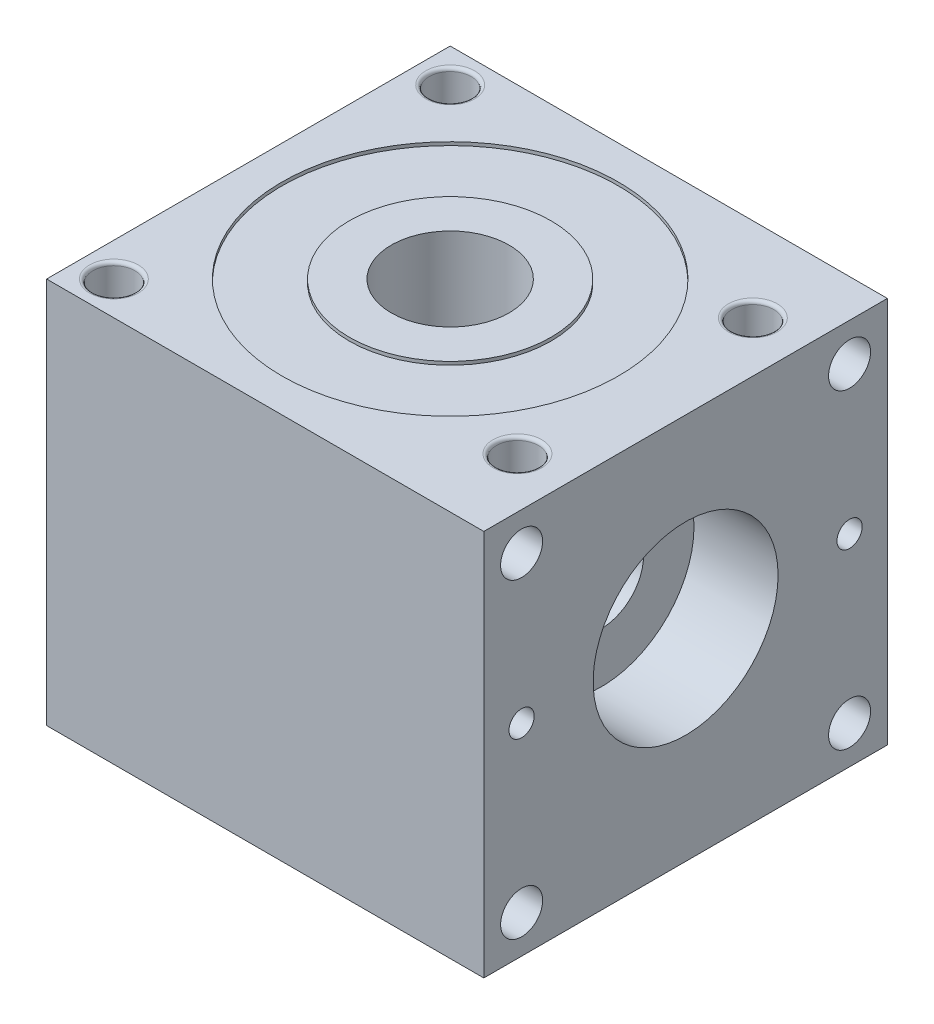
SolidWorks part; units mm, degrees
material "7079 Alloy"
ref_plane "Front Plane" through (0, 0, 0) normal (0, 0, 1) x (1, 0, 0)
ref_plane "Top Plane" through (0, 0, 0) normal (0, 1, 0) x (1, 0, 0)
ref_plane "Right Plane" through (0, 0, 0) normal (1, 0, 0) x (0, 0, -1)
sketch "Sketch1" plane through (0, 0, 0) normal (0, 1, 0) x (1, 0, 0)
  line L1 (0, 0) -> (82.55, 0)
  line L2 (0, 0) -> (0, -76.2)
  line L3 (0, -76.2) -> (82.55, -76.2)
  line L4 (82.55, 0) -> (82.55, -76.2)
  dimension "D1" = 82.55
extrude "Extrude1" add sketch "Sketch1" along normal blind 73.025
sketch "Sketch2" plane through (0, 73.025, 0) normal (0, 1, 0) x (-1, 0, 0)
  line L0 (-82.55, 0) -> (0, 0) construction
  line L1 (0, 0) -> (0, 76.2) construction
  line L2 (0, 76.2) -> (-82.55, 76.2) construction
  circle A0 centre (-38.1565, 38.1662) radius 10.16
  circle A1 centre (-6.35, 6.35) radius 3.9688
  circle A2 centre (-6.35, 69.8478) radius 3.9687
  circle A3 centre (-73.025, 15.875) radius 3.9688
  circle A4 centre (-73.025, 60.325) radius 3.9688
  dimension "D3" = 20.32
  dimension "D6" = 7.9375
  dimension "D1" = 38.1662
  dimension "D2" = 38.1565
  dimension "D4" = 6.35
  dimension "D5" = 6.35
  dimension "D7" = 6.3522
  dimension "D8" = 6.35
  dimension "D9" = 15.875
  dimension "D10" = 73.025
  dimension "D11" = 15.875
extrude "Cut-Extrude1" cut sketch "Sketch2" against normal blind 73.025
sketch "Sketch3" plane through (0, 73.025, 0) normal (0, 1, 0) x (-1, 0, 0)
  line L0 (-82.55, 0) -> (0, 0) construction
  line L1 (0, 0) -> (0, 76.2) construction
  circle A0 centre (-38.1, 38.1) radius 31.75
  circle A1 centre (-38.1, 38.1) radius 19.05
  dimension "D3" = 63.5
  dimension "D4" = 38.1
  dimension "D1" = 38.1
  dimension "D2" = 38.1
sketch "Sketch5" plane through (0, 0, 0) normal (0, -1, 0) x (1, 0, 0)
  circle A0 centre (38.1777, 38.1) radius 20.3862
extrude "Cut-Extrude2" cut sketch "Sketch5" against normal blind 8.6741
sketch "Sketch6" plane through (0, 0, 0) normal (-1, 0, 0) x (0, 0, 1)
  line L0 (0, 73.025) -> (0, 0) construction
  line L1 (76.2, 73.025) -> (76.2, 0) construction
  circle A0 centre (15.875, 38.1) radius 3.9688
  circle A1 centre (60.325, 38.1) radius 3.9688
  point P2 (0, 36.5125)
  dimension "D1" = 7.9375
  dimension "D2" = 34.925
  dimension "D3" = 15.875
  dimension "D4" = 15.875
extrude "Cut-Extrude3" cut sketch "Sketch6" against normal blind 15.875
fillet "Fillet1" radius 0.635 10 edges at (0, 38.1, 19.8438) (0, 38.1, 64.2938) (6.35, 0, 10.3187) (6.35, 0, 73.8166) (73.025, 0, 19.8438) (73.025, 0, 64.2938) (73.025, 73.025, 64.2938) (73.025, 73.025, 19.8438) (6.35, 73.025, 73.8166) (6.35, 73.025, 10.3187)
extrude "Cut-Extrude4" cut sketch "Sketch3" against normal blind 0.635
sketch "Sketch7" plane through (82.55, 0, 0) normal (1, 0, 0) x (0, 0, -1)
  line L0 (-76.2, 73.025) -> (0, 73.025) construction
  line L1 (-76.2, 0) -> (0, 0) construction
  line L2 (-76.2, 73.025) -> (-76.2, 0) construction
  line L4 (0, 73.025) -> (0, 0) construction
  circle A0 centre (-38.1, 38.1) radius 17.4625
  circle A1 centre (-69.0626, 65.8876) radius 3.9687
  circle A2 centre (-7.1374, 65.8876) radius 3.9687
  circle A3 centre (-69.0626, 7.1377) radius 3.9687
  circle A4 centre (-7.1374, 7.1377) radius 3.9687
  circle A5 centre (-69.0626, 38.1) radius 2.3813
  circle A6 centre (-7.1374, 38.1) radius 2.3813
  dimension "D4" = 34.925
  dimension "D7" = 7.9375
  dimension "D10" = 7.9375
  dimension "D11" = 7.9375
  dimension "D13" = 7.9375
  dimension "D14" = 7.1374
  dimension "D16" = 4.7625
  dimension "D17" = 4.7625
  dimension "D19" = 7.1374
  dimension "D1" = 34.925
  dimension "D2" = 38.1
  dimension "D3" = 38.1
  dimension "D5" = 7.1374
  dimension "D6" = 7.1374
  dimension "D8" = 69.0626
  dimension "D9" = 65.8873
  dimension "D12" = 7.1374
  dimension "D15" = 34.925
  dimension "D18" = 34.925
  dimension "D20" = 65.8873
  dimension "D21" = 7.1374
  dimension "D22" = 69.0626
extrude "Cut-Extrude5" cut sketch "Sketch7" against normal blind 15.875
sketch "Sketch8" plane through (82.55, 0, 0) normal (1, 0, 0) x (0, 0, -1)
  line L0 (-76.2, 73.025) -> (0, 73.025) construction
  line L1 (-76.2, 73.025) -> (-76.2, 0) construction
  circle A0 centre (-38.1, 38.1) radius 7.9375
  dimension "D1" = 15.875
  dimension "D2" = 34.925
  dimension "D3" = 38.1
extrude "Cut-Extrude6" cut sketch "Sketch8" against normal blind 50.8
sketch "Sketch9" plane through (0, 73.025, 0) normal (0, 1, 0) x (-1, 0, 0)
  circle A0 centre (-38.1, 38.1) radius 11.1125
  dimension "D1" = 22.225
extrude "Cut-Extrude7" cut sketch "Sketch9" against normal blind 57.15
